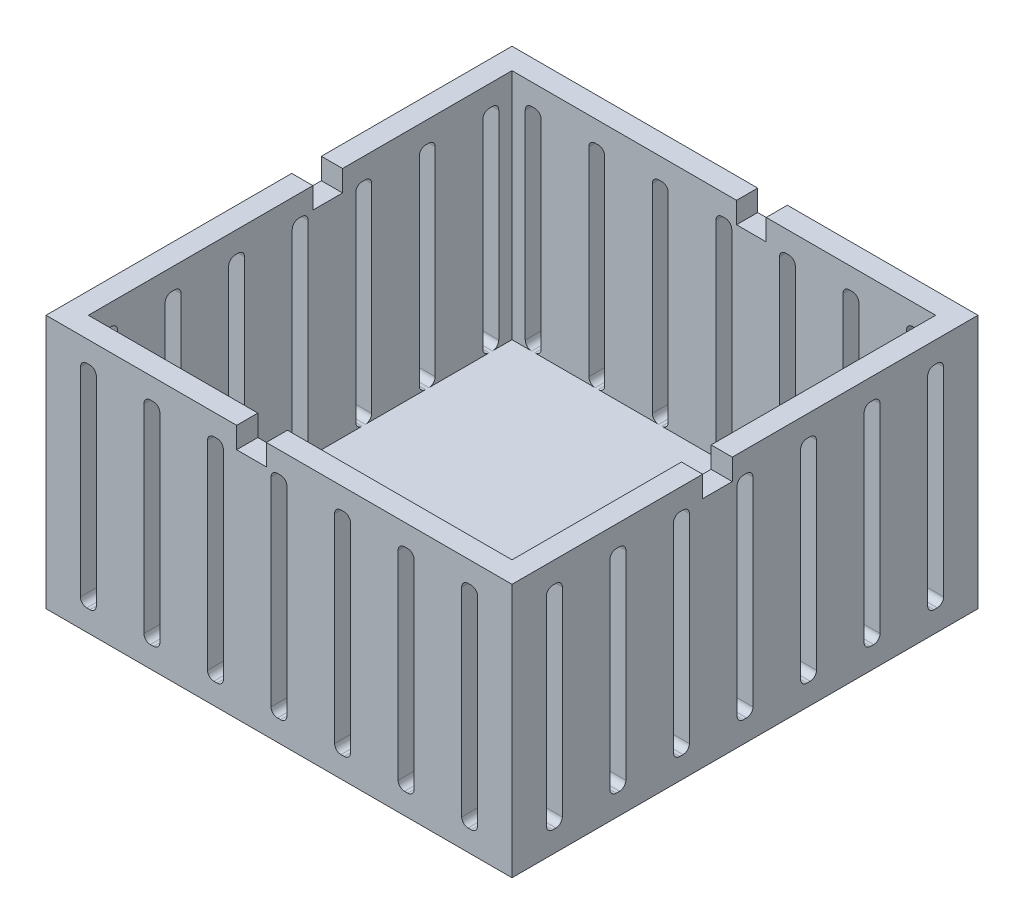
SolidWorks part; units mm, degrees
ref_plane "Front Plane" through (0, 0, 0) normal (0, 0, 1) x (1, 0, 0)
ref_plane "Top Plane" through (0, 0, 0) normal (0, 1, 0) x (1, 0, 0)
ref_plane "Right Plane" through (0, 0, 0) normal (1, 0, 0) x (0, 0, -1)
sketch "Sketch2" plane through (0, 0, 0) normal (0, 1, 0) x (1, 0, 0)
  line L1 (0, 0) -> (55.88, 0)
  line L2 (0, 0) -> (0, -55.88)
  line L3 (0, -55.88) -> (55.88, -55.88)
  line L4 (55.88, 0) -> (55.88, -55.88)
  dimension "D1" = 55.88
  dimension "D2" = 55.88
extrude "Boss-Extrude1" add sketch "Sketch2" along normal blind 30.48
sketch "Sketch3" plane through (0, 30.48, 0) normal (0, 1, 0) x (1, 0, 0)
  line L0 (0, 0) -> (0, -55.88) construction
  line L1 (2.54, -2.54) -> (53.34, -2.54)
  line L2 (2.54, -2.54) -> (2.54, -53.34)
  line L3 (2.54, -53.34) -> (53.34, -53.34)
  line L4 (53.34, -2.54) -> (53.34, -53.34)
  line L5 (55.88, 0) -> (0, 0) construction
  dimension "D1" = 50.8
  dimension "D2" = 50.8
  dimension "D3" = 2.54
  dimension "D4" = 2.54
extrude "Cut-Extrude1" cut sketch "Sketch3" against normal blind 27.94
sketch "Sketch4" plane through (0, 0, 55.88) normal (0, 0, 1) x (1, 0, 0)
  line L0 (0, 30.48) -> (55.88, 30.48) construction
  line L1 (27.7495, 27.94) -> (28.1305, 27.94)
  line L2 (26.9875, 27.178) -> (26.9875, 3.302)
  line L3 (27.7495, 2.54) -> (28.1305, 2.54)
  line L4 (28.8925, 27.178) -> (28.8925, 3.302)
  line L5 (34.6075, 27.178) -> (34.6075, 3.302)
  line L6 (35.3695, 27.94) -> (35.7505, 27.94)
  line L7 (36.5125, 27.178) -> (36.5125, 3.302)
  line L8 (35.3695, 2.54) -> (35.7505, 2.54)
  line L9 (42.2275, 27.178) -> (42.2275, 3.302)
  line L10 (42.9895, 27.94) -> (43.3705, 27.94)
  line L11 (44.1325, 27.178) -> (44.1325, 3.302)
  line L12 (42.9895, 2.54) -> (43.3705, 2.54)
  line L13 (49.8475, 27.178) -> (49.8475, 3.302)
  line L14 (50.6095, 27.94) -> (50.9905, 27.94)
  line L15 (51.7525, 27.178) -> (51.7525, 3.302)
  line L16 (50.6095, 2.54) -> (50.9905, 2.54)
  line L21 (19.3675, 27.178) -> (19.3675, 3.302)
  line L22 (20.1295, 27.94) -> (20.5105, 27.94)
  line L23 (21.2725, 27.178) -> (21.2725, 3.302)
  line L24 (20.1295, 2.54) -> (20.5105, 2.54)
  line L25 (11.7475, 27.178) -> (11.7475, 3.302)
  line L26 (12.5095, 27.94) -> (12.8905, 27.94)
  line L27 (13.6525, 27.178) -> (13.6525, 3.302)
  line L28 (12.5095, 2.54) -> (12.8905, 2.54)
  line L29 (4.1275, 27.178) -> (4.1275, 3.302)
  line L30 (4.8895, 27.94) -> (5.2705, 27.94)
  line L31 (6.0325, 27.178) -> (6.0325, 3.302)
  line L32 (4.8895, 2.54) -> (5.2705, 2.54)
  line L37 (-3.4925, 27.94) -> (-3.4925, 2.54) [skipped]
  line L38 (-3.4925, 27.94) -> (-1.5875, 27.94) [skipped]
  line L39 (-1.5875, 27.94) -> (-1.5875, 2.54) [skipped]
  line L40 (-3.4925, 2.54) -> (-1.5875, 2.54) [skipped]
  line L41 (57.4675, 27.94) -> (59.3725, 27.94) [skipped]
  line L42 (59.3725, 27.94) -> (59.3725, 2.54) [skipped]
  line L43 (57.4675, 2.54) -> (59.3725, 2.54) [skipped]
  line L44 (57.4675, 27.94) -> (57.4675, 2.54) [skipped]
  line L45 (0, 0) -> (55.88, 0) construction
  arc A0 (51.7525, 3.302) -> (50.9905, 2.54) centre (50.9905, 3.302) cw
  arc A1 (49.8475, 3.302) -> (50.6095, 2.54) centre (50.6095, 3.302) ccw
  arc A2 (50.9905, 27.94) -> (51.7525, 27.178) centre (50.9905, 27.178) cw
  arc A3 (49.8475, 27.178) -> (50.6095, 27.94) centre (50.6095, 27.178) cw
  arc A4 (43.3705, 27.94) -> (44.1325, 27.178) centre (43.3705, 27.178) cw
  arc A5 (42.2275, 27.178) -> (42.9895, 27.94) centre (42.9895, 27.178) cw
  arc A6 (44.1325, 3.302) -> (43.3705, 2.54) centre (43.3705, 3.302) cw
  arc A7 (42.2275, 3.302) -> (42.9895, 2.54) centre (42.9895, 3.302) ccw
  arc A8 (36.5125, 3.302) -> (35.7505, 2.54) centre (35.7505, 3.302) cw
  arc A9 (34.6075, 3.302) -> (35.3695, 2.54) centre (35.3695, 3.302) ccw
  arc A10 (35.7505, 27.94) -> (36.5125, 27.178) centre (35.7505, 27.178) cw
  arc A11 (34.6075, 27.178) -> (35.3695, 27.94) centre (35.3695, 27.178) cw
  arc A12 (5.2705, 27.94) -> (6.0325, 27.178) centre (5.2705, 27.178) cw
  arc A13 (4.1275, 27.178) -> (4.8895, 27.94) centre (4.8895, 27.178) cw
  arc A14 (4.1275, 3.302) -> (4.8895, 2.54) centre (4.8895, 3.302) ccw
  arc A15 (6.0325, 3.302) -> (5.2705, 2.54) centre (5.2705, 3.302) cw
  arc A16 (13.6525, 3.302) -> (12.8905, 2.54) centre (12.8905, 3.302) cw
  arc A17 (11.7475, 3.302) -> (12.5095, 2.54) centre (12.5095, 3.302) ccw
  arc A18 (12.8905, 27.94) -> (13.6525, 27.178) centre (12.8905, 27.178) cw
  arc A19 (11.7475, 27.178) -> (12.5095, 27.94) centre (12.5095, 27.178) cw
  arc A20 (20.5105, 27.94) -> (21.2725, 27.178) centre (20.5105, 27.178) cw
  arc A21 (19.3675, 27.178) -> (20.1295, 27.94) centre (20.1295, 27.178) cw
  arc A22 (19.3675, 3.302) -> (20.1295, 2.54) centre (20.1295, 3.302) ccw
  arc A23 (21.2725, 3.302) -> (20.5105, 2.54) centre (20.5105, 3.302) cw
  arc A24 (28.1305, 2.54) -> (28.8925, 3.302) centre (28.1305, 3.302) ccw
  arc A25 (26.9875, 3.302) -> (27.7495, 2.54) centre (27.7495, 3.302) ccw
  arc A26 (27.7495, 27.94) -> (26.9875, 27.178) centre (27.7495, 27.178) ccw
  arc A27 (28.1305, 27.94) -> (28.8925, 27.178) centre (28.1305, 27.178) cw
  point P6 (27.94, 30.48)
  point P7 (27.94, 27.94)
  point P100 (28.8925, 2.54)
  point P103 (26.9875, 2.54)
  dimension "D8" = 0.762
  dimension "D1" = 1.905
  dimension "D4" = 7.62
  dimension "D5" = 7.62
  dimension "D6" = 2.54
  dimension "D7" = 2.54
  dimension "D2" = 5
  dimension "D3" = 5
extrude "Cut-Extrude2" cut sketch "Sketch4" against normal up to surface (55.88 mm away) up to face at (27.94, 15.24, 0)
sketch "Sketch5" plane through (0, 0, 0) normal (-1, 0, 0) x (0, 0, 1)
  line L0 (0, 30.48) -> (55.88, 30.48) construction
  line L1 (27.7495, 27.94) -> (28.1305, 27.94)
  line L2 (26.9875, 27.178) -> (26.9875, 3.302)
  line L3 (27.7495, 2.54) -> (28.1305, 2.54)
  line L4 (28.8925, 27.178) -> (28.8925, 3.302)
  line L5 (0, 0) -> (55.88, 0) construction
  line L6 (34.6075, 27.178) -> (34.6075, 3.302)
  line L7 (35.3695, 27.94) -> (35.7505, 27.94)
  line L8 (36.5125, 27.178) -> (36.5125, 3.302)
  line L9 (35.3695, 2.54) -> (35.7505, 2.54)
  line L10 (42.2275, 27.178) -> (42.2275, 3.302)
  line L11 (42.9895, 27.94) -> (43.3705, 27.94)
  line L12 (44.1325, 27.178) -> (44.1325, 3.302)
  line L13 (42.9895, 2.54) -> (43.3705, 2.54)
  line L14 (49.8475, 27.178) -> (49.8475, 3.302)
  line L15 (50.6095, 27.94) -> (50.9905, 27.94)
  line L16 (51.7525, 27.178) -> (51.7525, 3.302)
  line L17 (50.6095, 2.54) -> (50.9905, 2.54)
  line L18 (26.9875, 27.94) -> (26.9875, 2.54)
  line L19 (26.9875, 27.94) -> (28.8925, 27.94)
  line L20 (28.8925, 27.94) -> (28.8925, 2.54)
  line L21 (26.9875, 2.54) -> (28.8925, 2.54)
  line L22 (34.6075, 27.94) -> (34.6075, 2.54)
  line L23 (34.6075, 27.94) -> (36.5125, 27.94)
  line L24 (36.5125, 27.94) -> (36.5125, 2.54)
  line L25 (34.6075, 2.54) -> (36.5125, 2.54)
  line L26 (42.2275, 27.94) -> (42.2275, 2.54)
  line L27 (42.2275, 27.94) -> (44.1325, 27.94)
  line L28 (44.1325, 27.94) -> (44.1325, 2.54)
  line L29 (42.2275, 2.54) -> (44.1325, 2.54)
  line L30 (19.3675, 27.178) -> (19.3675, 3.302)
  line L31 (20.1295, 27.94) -> (20.5105, 27.94)
  line L32 (21.2725, 27.178) -> (21.2725, 3.302)
  line L33 (20.1295, 2.54) -> (20.5105, 2.54)
  line L34 (26.9875, 27.94) -> (26.9875, 2.54)
  line L35 (26.9875, 27.94) -> (28.8925, 27.94)
  line L36 (28.8925, 27.94) -> (28.8925, 2.54)
  line L37 (26.9875, 2.54) -> (28.8925, 2.54)
  line L38 (34.6075, 27.94) -> (34.6075, 2.54)
  line L39 (34.6075, 27.94) -> (36.5125, 27.94)
  line L40 (36.5125, 27.94) -> (36.5125, 2.54)
  line L41 (34.6075, 2.54) -> (36.5125, 2.54)
  line L42 (11.7475, 27.178) -> (11.7475, 3.302)
  line L43 (12.5095, 27.94) -> (12.8905, 27.94)
  line L44 (13.6525, 27.178) -> (13.6525, 3.302)
  line L45 (12.5095, 2.54) -> (12.8905, 2.54)
  line L46 (19.3675, 27.94) -> (19.3675, 2.54)
  line L47 (19.3675, 27.94) -> (21.2725, 27.94)
  line L48 (21.2725, 27.94) -> (21.2725, 2.54)
  line L49 (19.3675, 2.54) -> (21.2725, 2.54)
  line L50 (26.9875, 27.94) -> (26.9875, 2.54)
  line L51 (26.9875, 27.94) -> (28.8925, 27.94)
  line L52 (28.8925, 27.94) -> (28.8925, 2.54)
  line L53 (26.9875, 2.54) -> (28.8925, 2.54)
  line L54 (19.3675, 27.94) -> (19.3675, 2.54)
  line L55 (19.3675, 27.94) -> (21.2725, 27.94)
  line L56 (21.2725, 27.94) -> (21.2725, 2.54)
  line L57 (19.3675, 2.54) -> (21.2725, 2.54)
  line L58 (11.7475, 27.94) -> (11.7475, 2.54)
  line L59 (11.7475, 27.94) -> (13.6525, 27.94)
  line L60 (13.6525, 27.94) -> (13.6525, 2.54)
  line L61 (11.7475, 2.54) -> (13.6525, 2.54)
  line L62 (4.1275, 27.178) -> (4.1275, 3.302)
  line L63 (4.8895, 27.94) -> (5.2705, 27.94)
  line L64 (6.0325, 27.178) -> (6.0325, 3.302)
  line L65 (4.8895, 2.54) -> (5.2705, 2.54)
  arc A0 (51.7525, 3.302) -> (50.9905, 2.54) centre (50.9905, 3.302) cw
  arc A1 (49.8475, 3.302) -> (50.6095, 2.54) centre (50.6095, 3.302) ccw
  arc A2 (44.1325, 3.302) -> (43.3705, 2.54) centre (43.3705, 3.302) cw
  arc A3 (42.2275, 3.302) -> (42.9895, 2.54) centre (42.9895, 3.302) ccw
  arc A4 (36.5125, 3.302) -> (35.7505, 2.54) centre (35.7505, 3.302) cw
  arc A5 (34.6075, 3.302) -> (35.3695, 2.54) centre (35.3695, 3.302) ccw
  arc A6 (28.1305, 2.54) -> (28.8925, 3.302) centre (28.1305, 3.302) ccw
  arc A7 (26.9875, 3.302) -> (27.7495, 2.54) centre (27.7495, 3.302) ccw
  arc A8 (21.2725, 3.302) -> (20.5105, 2.54) centre (20.5105, 3.302) cw
  arc A9 (19.3675, 3.302) -> (20.1295, 2.54) centre (20.1295, 3.302) ccw
  arc A10 (13.6525, 3.302) -> (12.8905, 2.54) centre (12.8905, 3.302) cw
  arc A11 (11.7475, 3.302) -> (12.5095, 2.54) centre (12.5095, 3.302) ccw
  arc A12 (6.0325, 3.302) -> (5.2705, 2.54) centre (5.2705, 3.302) cw
  arc A13 (4.1275, 3.302) -> (4.8895, 2.54) centre (4.8895, 3.302) ccw
  arc A14 (50.9905, 27.94) -> (51.7525, 27.178) centre (50.9905, 27.178) cw
  arc A15 (49.8475, 27.178) -> (50.6095, 27.94) centre (50.6095, 27.178) cw
  arc A16 (43.3705, 27.94) -> (44.1325, 27.178) centre (43.3705, 27.178) cw
  arc A17 (42.2275, 27.178) -> (42.9895, 27.94) centre (42.9895, 27.178) cw
  arc A18 (35.7505, 27.94) -> (36.5125, 27.178) centre (35.7505, 27.178) cw
  arc A19 (34.6075, 27.178) -> (35.3695, 27.94) centre (35.3695, 27.178) cw
  arc A20 (28.1305, 27.94) -> (28.8925, 27.178) centre (28.1305, 27.178) cw
  arc A21 (27.7495, 27.94) -> (26.9875, 27.178) centre (27.7495, 27.178) ccw
  arc A22 (20.5105, 27.94) -> (21.2725, 27.178) centre (20.5105, 27.178) cw
  arc A23 (19.3675, 27.178) -> (20.1295, 27.94) centre (20.1295, 27.178) cw
  arc A24 (12.8905, 27.94) -> (13.6525, 27.178) centre (12.8905, 27.178) cw
  arc A25 (11.7475, 27.178) -> (12.5095, 27.94) centre (12.5095, 27.178) cw
  arc A26 (5.2705, 27.94) -> (6.0325, 27.178) centre (5.2705, 27.178) cw
  arc A27 (4.1275, 27.178) -> (4.8895, 27.94) centre (4.8895, 27.178) cw
  point P8 (27.94, 30.48)
  point P9 (27.94, 27.94)
  point P84 (28.8925, 2.54)
  point P87 (26.9875, 2.54)
  dimension "D6" = 0.762
  dimension "D1" = 1.905
  dimension "D2" = 2.54
  dimension "D3" = 2.54
  dimension "D4" = 4
  dimension "D5" = 4
extrude "Cut-Extrude3" cut sketch "Sketch5" against normal up to surface (55.88 mm away) contours L10 L13 L12 L11 | L6 L9 L8 L7 | L14 L17 L16 L15 | L4 A6 L3 A7 L2 A21 L1 A20 | L32 A8 L33 A9 L30 A23 L31 A22 | L44 A10 L45 A11 L42 A25 L43 A24 | L64 A12 L65 A13 L62 A27 L63 A26
sketch "Sketch6" plane through (0, 0, 0) normal (-1, 0, 0) x (0, 0, 1)
  line L0 (22.86, 30.48) -> (22.86, 27.94)
  line L2 (0, 30.48) -> (55.88, 30.48) construction
  line L3 (22.86, 27.94) -> (26.416, 27.94)
  line L4 (26.416, 27.94) -> (26.416, 30.48)
  line L5 (26.416, 30.48) -> (22.86, 30.48)
  line L6 (0, 30.48) -> (0, 0) construction
  dimension "D1" = 3.556
  dimension "D2" = 2.54
  dimension "D3" = 22.86
extrude "Cut-Extrude4" cut sketch "Sketch6" against normal up to surface (2.54 mm away) up to face at (2.54, 15.3247, 27.94)
sketch "Sketch7" plane through (0, 0, 0) normal (0, 0, -1) x (-1, 0, 0)
  line L0 (-33.02, 30.48) -> (-33.02, 27.94)
  line L1 (-55.88, 30.48) -> (0, 30.48) construction
  line L2 (-33.02, 27.94) -> (-29.464, 27.94)
  line L3 (-29.464, 27.94) -> (-29.464, 30.48)
  line L4 (-29.464, 30.48) -> (-33.02, 30.48)
  line L5 (-55.88, 30.48) -> (-55.88, 0) construction
  dimension "D1" = 2.54
  dimension "D2" = 3.556
  dimension "D3" = 22.86
extrude "Cut-Extrude5" cut sketch "Sketch7" against normal up to surface (2.54 mm away) up to face at (27.94, 15.3247, 2.54)
sketch "Sketch8" plane through (55.88, 0, 0) normal (1, 0, 0) x (0, 0, -1)
  line L0 (-55.88, 30.48) -> (0, 30.48) construction
  line L1 (-33.02, 30.48) -> (-29.464, 30.48)
  line L2 (-33.02, 30.48) -> (-33.02, 27.94)
  line L3 (-33.02, 27.94) -> (-29.464, 27.94)
  line L4 (-29.464, 30.48) -> (-29.464, 27.94)
  line L5 (-55.88, 30.48) -> (-55.88, 0) construction
  dimension "D1" = 3.556
  dimension "D2" = 2.54
  dimension "D3" = 22.86
extrude "Cut-Extrude6" cut sketch "Sketch8" against normal up to surface (2.54 mm away) up to face at (53.34, 15.3247, 27.94)
sketch "Sketch9" plane through (0, 0, 55.88) normal (0, 0, 1) x (1, 0, 0)
  line L0 (0, 30.48) -> (55.88, 30.48) construction
  line L1 (22.86, 30.48) -> (26.416, 30.48)
  line L2 (22.86, 30.48) -> (22.86, 27.94)
  line L3 (22.86, 27.94) -> (26.416, 27.94)
  line L4 (26.416, 30.48) -> (26.416, 27.94)
  line L5 (0, 30.48) -> (0, 0) construction
  dimension "D1" = 3.556
  dimension "D2" = 2.54
  dimension "D3" = 22.86
extrude "Cut-Extrude7" cut sketch "Sketch9" against normal up to surface (2.54 mm away) up to face at (27.94, 15.3247, 53.34)
